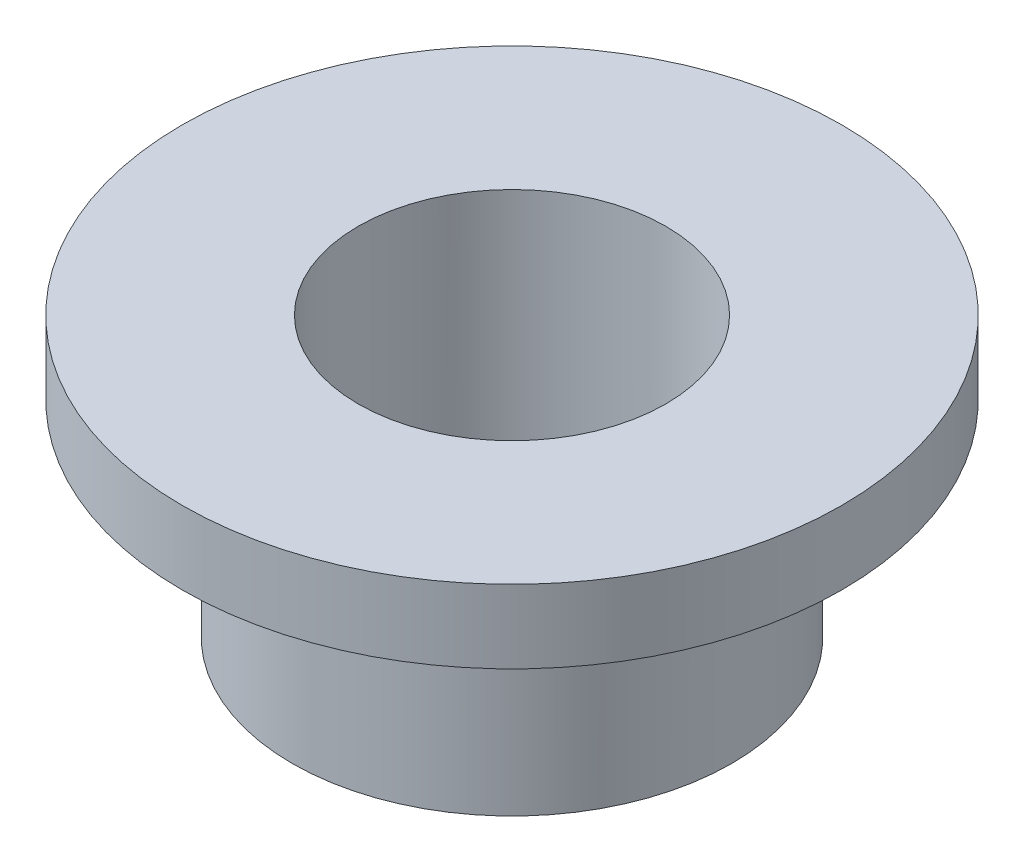
SolidWorks part; units mm, degrees
ref_plane "前视基准面" through (0, 0, 0) normal (0, 0, 1) x (1, 0, 0)
ref_plane "上视基准面" through (0, 0, 0) normal (0, 1, 0) x (1, 0, 0)
ref_plane "右视基准面" through (0, 0, 0) normal (1, 0, 0) x (0, 0, -1)
sketch "草图1" plane through (0, 0, 0) normal (0, 1, 0) x (1, 0, 0)
  circle A0 centre (0, 0) radius 4.5
  circle A1 centre (0, 0) radius 2.1
  dimension "D1" = 9
  dimension "D2" = 4.2
extrude "凸台-拉伸1" add sketch "草图1" along normal blind 1
sketch "草图2" plane through (0, 0, 0) normal (0, -1, 0) x (1, 0, 0)
  circle A0 centre (0, 0) radius 3
  circle A1 centre (0, 0) radius 2.1 construction
  circle A2 centre (0, 0) radius 2.1
  dimension "D1" = 6
extrude "凸台-拉伸2" add sketch "草图2" along normal blind 2.8
